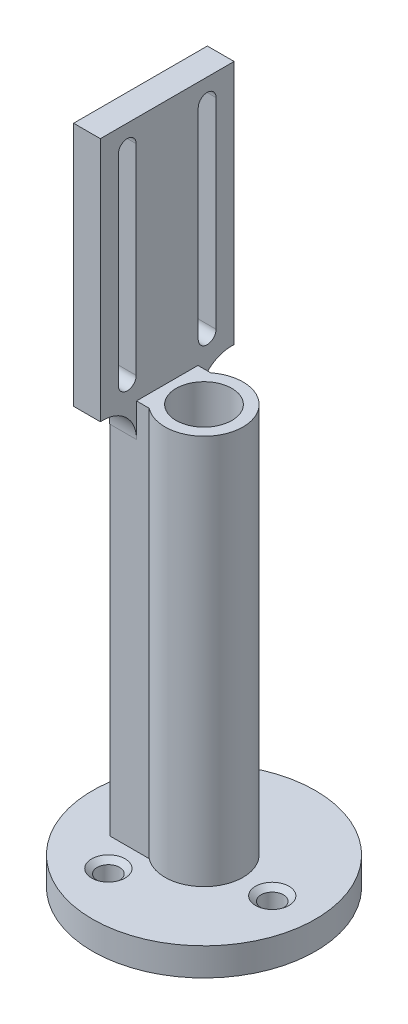
SolidWorks part; units mm, degrees
ref_plane "Front Plane" through (0, 0, 0) normal (0, 0, 1) x (1, 0, 0)
ref_plane "Top Plane" through (0, 0, 0) normal (0, 1, 0) x (1, 0, 0)
ref_plane "Right Plane" through (0, 0, 0) normal (1, 0, 0) x (0, 0, -1)
sketch "Sketch1" plane through (0, 0, 0) normal (0, 0, 1) x (1, 0, 0)
  line L0 (0, 131.177) -> (0, 0) construction
  line L1 (6.35, 19.05) -> (25.4, 19.05)
  line L2 (25.4, 19.05) -> (25.4, 25.4)
  line L3 (25.4, 25.4) -> (8.89, 25.4)
  line L4 (8.89, 25.4) -> (8.89, 114.3)
  line L8 (6.35, 114.3) -> (6.35, 19.05)
  line L9 (6.35, 114.3) -> (8.89, 114.3)
  dimension "D1" = 50.8
  dimension "D2" = 6.35
  dimension "D3" = 17.78
  dimension "D4" = 88.9
  dimension "D5" = 12.7
  dimension "D6" = 19.05
revolve "Revolve1" add sketch "Sketch1" angle 360 about L0
hole_wizard "1/4-20 Tapped Hole1" positions "Sketch8" profile "Sketch9" tap size "1/4-20" standard "ANSI Inch" end condition through all
sketch "Sketch8" plane through (0, 25.4, 0) normal (0, 1, 0) x (1, 0, 0)
  circle A0 centre (0, 0) radius 15.875 construction
  point P7 (-7.6595, 13.905)
  point P17 (15.8718, -0.3192)
  point P18 (-8.2123, -13.5858)
  dimension "D1" = 31.75
  dimension "D2" = 3
sketch "Sketch9" plane through (-8.2123, 25.4, 13.5858) normal (1, 0, 0) x (0, 0, 1)
  line L0 (0, 0) -> (0, 6.35)
  line L1 (0, 6.35) -> (2.5527, 6.35)
  line L2 (2.5527, 6.35) -> (2.5527, 1.055)
  line L3 (2.5527, 1.055) -> (3.81, 0)
  line L5 (3.81, 0) -> (0, 0)
  line L6 (-2.5527, 1.055) -> (-3.81, 0) construction
  line L11 (0, -6.35) -> (0, 107.95) construction
  dimension "Thru Tap Drill Dia." = 5.1054
  dimension "Thru Tap Drill Depth" = 6.35
  dimension "Near C'Sink Dia." = 7.62
  dimension "Near C'Sink Angle" = 100
cosmetic thread "Hole Thread1" parameters "D2"=6.35
cosmetic thread "Hole Thread2" parameters "D2"=6.35
cosmetic thread "Hole Thread3" parameters "D2"=6.35
sketch "Sketch12" plane through (0, 25.4, 0) normal (0, 1, 0) x (1, 0, 0)
  line L3 (-5.4802, -7) -> (-14.478, -7)
  line L4 (-14.478, -7) -> (-14.478, 7)
  line L5 (-14.478, 7) -> (-5.4802, 7)
  line L6 (-9.398, -7) -> (-9.398, 7) construction
  circle A1 centre (0, 0) radius 8.89 construction
  arc A5 (-5.4802, 7) -> (-5.4802, -7) centre (0, 0) ccw
  point P5 (-8.89, 0)
  point P10 (-14.478, 0)
  dimension "D3" = 5.08
  dimension "D2" = 0.508
  dimension "D1" = 14
extrude "Boss-Extrude1" add sketch "Sketch12" along normal blind 88.9
sketch "Sketch13" plane through (0, 114.3, 0) normal (0, 1, 0) x (1, 0, 0)
  line L0 (-14.478, 15.24) -> (-14.478, -15.24)
  line L2 (-14.478, -15.24) -> (-8.382, -15.24)
  line L3 (-8.382, -15.24) -> (-8.382, 15.24)
  line L4 (-8.382, 15.24) -> (-14.478, 15.24)
  line L5 (-14.478, 7) -> (-14.478, -7) construction
  point P3 (-14.478, 0)
  dimension "D1" = 6.096
  dimension "D2" = 30.48
extrude "Boss-Extrude2" add sketch "Sketch13" along normal blind 55.88
sketch "Sketch15" plane through (-8.382, 0, 0) normal (1, 0, 0) x (0, 0, -1)
  line L0 (0, 170.18) -> (0, 114.3) construction
  line L1 (-9.1, 119.38) -> (-9.1, 165.1) construction
  line L2 (-11.132, 119.38) -> (-11.132, 165.1)
  line L3 (-7.068, 119.38) -> (-7.068, 165.1)
  line L4 (-15.24, 170.18) -> (15.24, 170.18) construction
  line L5 (8.89, 114.3) -> (-8.89, 114.3) construction
  line L6 (-15.24, 114.3) -> (-7, 114.3) construction
  line L7 (9.1, 119.38) -> (9.1, 165.1) construction
  line L8 (11.132, 119.38) -> (11.132, 165.1)
  line L9 (7.068, 119.38) -> (7.068, 165.1)
  arc A0 (-11.132, 119.38) -> (-7.068, 119.38) centre (-9.1, 119.38) ccw
  arc A1 (-7.068, 165.1) -> (-11.132, 165.1) centre (-9.1, 165.1) ccw
  arc A2 (11.132, 119.38) -> (7.068, 119.38) centre (9.1, 119.38) cw
  arc A3 (7.068, 165.1) -> (11.132, 165.1) centre (9.1, 165.1) cw
  point P5 (-9.1, 142.24)
  point P15 (0, 142.24)
  point P20 (9.1, 142.24)
  dimension "D1" = 2.032
  dimension "D3" = 5.08
  dimension "D2" = 9.1
extrude "Cut-Extrude1" cut sketch "Sketch15" against normal up to next
fillet "Fillet1" radius 7.62 2 edges at (-11.43, 114.3, -7) (-11.43, 114.3, 7)
